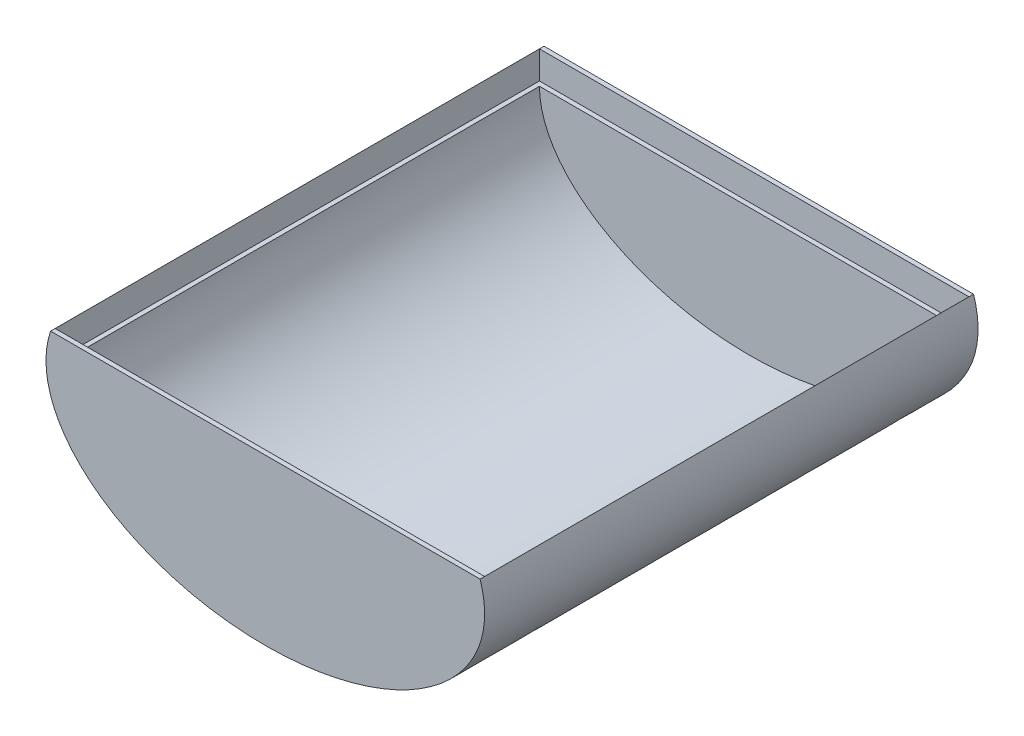
SolidWorks part; units mm, degrees
ref_plane "Front Plane" through (0, 0, 0) normal (0, 0, 1) x (1, 0, 0)
ref_plane "Top Plane" through (0, 0, 0) normal (0, 1, 0) x (1, 0, 0)
ref_plane "Right Plane" through (0, 0, 0) normal (1, 0, 0) x (0, 0, -1)
sketch "Sketch1" plane through (0, 0, 0) normal (0, 0, 1) x (1, 0, 0)
  ellipse E1 centre (0, 0) end of major axis (-15.24, 0) minor radius 9.525
extrude "Boss-Extrude2" add sketch "Sketch1" along normal blind 34.29
sketch "Sketch3" plane through (0, 0, 34.29) normal (0, 0, 1) x (1, 0, 0)
  ellipse E0 centre (0, 0) end of major axis (14.605, 0) minor radius 8.89
  ellipse E1 centre (0, 0) end of major axis (-15.24, 0) minor radius 9.525 construction
  dimension "D1" = 8.89
  dimension "D2" = 14.605
extrude "Cut-Extrude1" cut sketch "Sketch3" against normal blind 33.02 from offset 0.635 offset against normal yes
sketch "Sketch4" plane through (0, 0, 34.29) normal (0, 0, 1) x (1, 0, 0)
  line L0 (14.9225, 0) -> (14.9225, 203.2)
  line L1 (14.9225, 0) -> (-14.9225, 0)
  line L2 (0, 0) -> (0, 203.2)
  line L3 (14.9225, 203.2) -> (-14.9225, 203.2)
  line L4 (-14.9225, 0) -> (-14.9225, 203.2)
  ellipse M6 centre (0, 0) end of major axis (-15.24, 0) minor radius 9.525
  dimension "D1" = 14.9225
  dimension "D2" = 203.2
extrude "Cut-Extrude3" cut sketch "Sketch4" against normal blind 32.7025 from offset 0.635 contours L4 L1 L2 M6 | L2 L1 L0 M6 offset against normal yes
sketch "Sketch6" plane through (0, 0, 33.655) normal (0, 0, -1) x (-1, 0, 0)
  line L1 (-14.9225, 1.9341) -> (17.144, 1.9341)
  line L2 (-14.9225, 1.9341) -> (-14.9225, 11.0536)
  line L3 (-14.9225, 11.0536) -> (17.144, 11.0536)
  line L4 (17.144, 1.9341) -> (17.144, 11.0536)
extrude "Cut-Extrude4" cut sketch "Sketch6" against normal blind 32.7025 and the other way blind 40.3225
sketch "Sketch7" plane through (0, 1.9341, 0) normal (0, 1, 0) x (1, 0, 0)
  line L0 (14.9225, -33.655) -> (14.9225, -34.29) construction
  line L1 (-14.5945, -0.3175) -> (14.9225, -0.3175)
  line L2 (-14.5945, -0.3175) -> (-14.5945, -33.9725)
  line L3 (-14.5945, -33.9725) -> (14.9225, -33.9725)
  line L4 (14.9225, -0.3175) -> (14.9225, -33.9725)
  line L5 (14.9225, 0) -> (-14.9225, 0) construction
  line L7 (14.9225, -34.29) -> (-14.9225, -34.29) construction
  dimension "D1" = 0.3175
  dimension "D2" = 0.3175
extrude "Cut-Extrude5" cut sketch "Sketch7" against normal up to surface (1.9341 mm away) up to face at (-14.7637, 0, 17.3038)
sketch "Sketch8" plane through (0, 1.9341, 0) normal (0, 1, 0) x (1, 0, 0)
  line L0 (-14.5945, -33.655) -> (-14.9225, -33.655) construction
  line L1 (-14.5945, -33.655) -> (-14.9225, -33.655)
  line L2 (-14.5945, -33.655) -> (-14.5945, -33.9725)
  line L3 (-14.5945, -33.9725) -> (-14.9225, -33.9725)
  line L4 (-14.9225, -33.655) -> (-14.9225, -33.9725)
  line L5 (-14.5945, -33.655) -> (-14.5945, -33.9725) construction
  line L6 (-14.9225, -33.655) -> (-14.9225, -34.29) construction
extrude "Cut-Extrude6" cut sketch "Sketch8" against normal up to surface (1.9341 mm away) up to face at (-14.7637, 0, 17.3038)
sketch "Sketch9" plane through (0, 1.9341, 0) normal (0, 1, 0) x (1, 0, 0)
  line L1 (-14.9225, -0.9525) -> (-14.5945, -0.9525)
  line L2 (-14.9225, -0.9525) -> (-14.9225, -0.3175)
  line L3 (-14.9225, -0.3175) -> (-14.5945, -0.3175)
  line L4 (-14.5945, -0.9525) -> (-14.5945, -0.3175)
extrude "Cut-Extrude7" cut sketch "Sketch9" against normal up to surface (1.9341 mm away) up to face at (-2.9189, 0, 13.9065)
